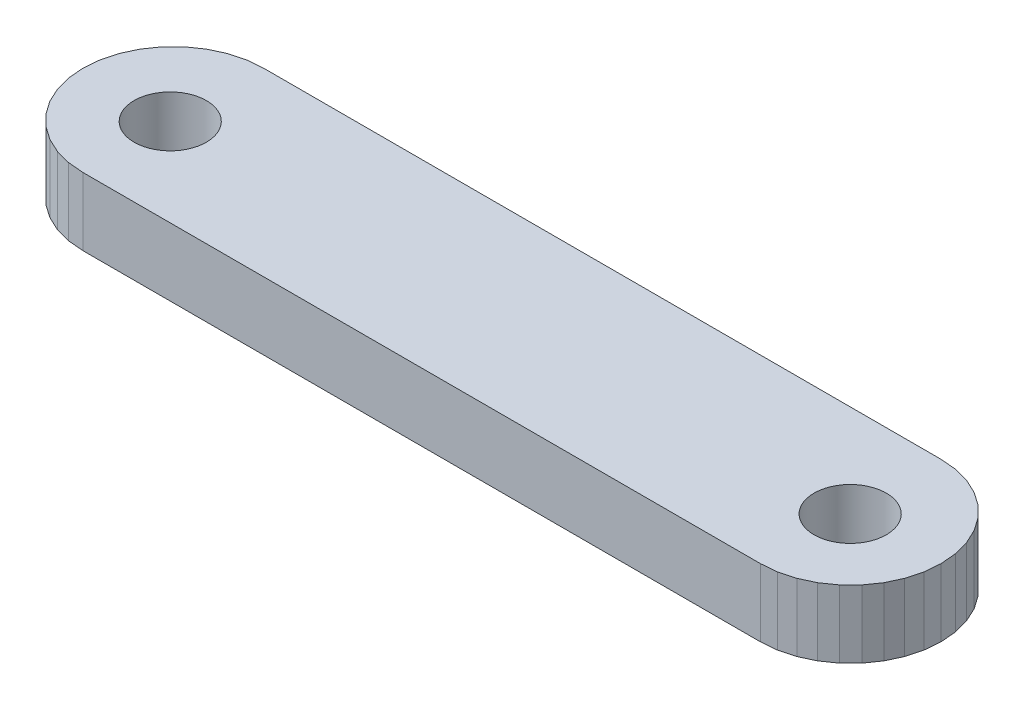
SolidWorks part; units mm, degrees
ref_plane "Front Plane" through (0, 0, 0) normal (0, 0, 1) x (1, 0, 0)
ref_plane "Top Plane" through (0, 0, 0) normal (0, 1, 0) x (1, 0, 0)
ref_plane "Right Plane" through (0, 0, 0) normal (1, 0, 0) x (0, 0, -1)
ref_plane "Plane1" through (0, 0, 0) normal (0, -1, 0) x (1, 0, 0)
sketch "Sketch1" plane through (0, 0, 0) normal (0, -1, 0) x (1, 0, 0)
  line L0 (3.3054, 0.0608) -> (4, 0)
  line L1 (4, 0) -> (34, 0)
  line L2 (34, 0) -> (34.6946, 0.0608)
  line L3 (34.6946, 0.0608) -> (35.3681, 0.2412)
  line L4 (35.3681, 0.2412) -> (36, 0.5359)
  line L5 (36, 0.5359) -> (36.5712, 0.9358)
  line L6 (36.5712, 0.9358) -> (37.0642, 1.4288)
  line L7 (37.0642, 1.4288) -> (37.4641, 2)
  line L8 (37.4641, 2) -> (37.7588, 2.6319)
  line L9 (37.7588, 2.6319) -> (37.9392, 3.3054)
  line L10 (37.9392, 3.3054) -> (38, 4)
  line L11 (38, 4) -> (37.9392, 4.6946)
  line L12 (37.9392, 4.6946) -> (37.7588, 5.3681)
  line L13 (37.7588, 5.3681) -> (37.4641, 6)
  line L14 (37.4641, 6) -> (37.0642, 6.5712)
  line L15 (37.0642, 6.5712) -> (36.5712, 7.0642)
  line L16 (36.5712, 7.0642) -> (36, 7.4641)
  line L17 (36, 7.4641) -> (35.3681, 7.7588)
  line L18 (35.3681, 7.7588) -> (34.6946, 7.9392)
  line L19 (34.6946, 7.9392) -> (34, 8)
  line L20 (34, 8) -> (4, 8)
  line L21 (4, 8) -> (3.3054, 7.9392)
  line L22 (3.3054, 7.9392) -> (2.6319, 7.7588)
  line L23 (2.6319, 7.7588) -> (2, 7.4641)
  line L24 (2, 7.4641) -> (1.4288, 7.0642)
  line L25 (1.4288, 7.0642) -> (0.9358, 6.5712)
  line L26 (0.9358, 6.5712) -> (0.5359, 6)
  line L27 (0.5359, 6) -> (0.2412, 5.3681)
  line L28 (0.2412, 5.3681) -> (0.0608, 4.6946)
  line L29 (0.0608, 4.6946) -> (0, 4)
  line L30 (0, 4) -> (0.0608, 3.3054)
  line L31 (0.0608, 3.3054) -> (0.2412, 2.6319)
  line L32 (0.2412, 2.6319) -> (0.5359, 2)
  line L33 (0.5359, 2) -> (0.9358, 1.4288)
  line L34 (0.9358, 1.4288) -> (1.4288, 0.9358)
  line L35 (1.4288, 0.9358) -> (2, 0.5359)
  line L36 (2, 0.5359) -> (2.6319, 0.2412)
  line L37 (2.6319, 0.2412) -> (3.3054, 0.0608)
  line L38 (32.3913, 2.6501) -> (32.1813, 2.95)
  line L39 (32.1813, 2.95) -> (32.0266, 3.2818)
  line L40 (32.0266, 3.2818) -> (31.9319, 3.6353)
  line L41 (31.9319, 3.6353) -> (31.9, 4)
  line L42 (31.9, 4) -> (31.9319, 4.3647)
  line L43 (31.9319, 4.3647) -> (32.0266, 4.7182)
  line L44 (32.0266, 4.7182) -> (32.1813, 5.05)
  line L45 (32.1813, 5.05) -> (32.3913, 5.3499)
  line L46 (32.3913, 5.3499) -> (32.6501, 5.6087)
  line L47 (32.6501, 5.6087) -> (32.95, 5.8187)
  line L48 (32.95, 5.8187) -> (33.2818, 5.9734)
  line L49 (33.2818, 5.9734) -> (33.6353, 6.0681)
  line L50 (33.6353, 6.0681) -> (34, 6.1)
  line L51 (34, 6.1) -> (34.3647, 6.0681)
  line L52 (34.3647, 6.0681) -> (34.7182, 5.9734)
  line L53 (34.7182, 5.9734) -> (35.05, 5.8187)
  line L54 (35.05, 5.8187) -> (35.3499, 5.6087)
  line L55 (35.3499, 5.6087) -> (35.6087, 5.3499)
  line L56 (35.6087, 5.3499) -> (35.8187, 5.05)
  line L57 (35.8187, 5.05) -> (35.9734, 4.7182)
  line L58 (35.9734, 4.7182) -> (36.0681, 4.3647)
  line L59 (36.0681, 4.3647) -> (36.1, 4)
  line L60 (36.1, 4) -> (36.0681, 3.6353)
  line L61 (36.0681, 3.6353) -> (35.9734, 3.2818)
  line L62 (35.9734, 3.2818) -> (35.8187, 2.95)
  line L63 (35.8187, 2.95) -> (35.6087, 2.6501)
  line L64 (35.6087, 2.6501) -> (35.3499, 2.3913)
  line L65 (35.3499, 2.3913) -> (35.05, 2.1813)
  line L66 (35.05, 2.1813) -> (34.7182, 2.0266)
  line L67 (34.7182, 2.0266) -> (34.3647, 1.9319)
  line L68 (34.3647, 1.9319) -> (34, 1.9)
  line L69 (34, 1.9) -> (33.6353, 1.9319)
  line L70 (33.6353, 1.9319) -> (33.2818, 2.0266)
  line L71 (33.2818, 2.0266) -> (32.95, 2.1813)
  line L72 (32.95, 2.1813) -> (32.6501, 2.3913)
  line L73 (32.6501, 2.3913) -> (32.3913, 2.6501)
  line L74 (5.6853, 2.5859) -> (5.4141, 2.3147)
  line L75 (5.4141, 2.3147) -> (5.1, 2.0947)
  line L76 (5.1, 2.0947) -> (4.7524, 1.9327)
  line L77 (4.7524, 1.9327) -> (4.382, 1.8334)
  line L78 (4.382, 1.8334) -> (4, 1.8)
  line L79 (4, 1.8) -> (3.618, 1.8334)
  line L80 (3.618, 1.8334) -> (3.2476, 1.9327)
  line L81 (3.2476, 1.9327) -> (2.9, 2.0947)
  line L82 (2.9, 2.0947) -> (2.5859, 2.3147)
  line L83 (2.5859, 2.3147) -> (2.3147, 2.5859)
  line L84 (2.3147, 2.5859) -> (2.0947, 2.9)
  line L85 (2.0947, 2.9) -> (1.9327, 3.2476)
  line L86 (1.9327, 3.2476) -> (1.8334, 3.618)
  line L87 (1.8334, 3.618) -> (1.8, 4)
  line L88 (1.8, 4) -> (1.8334, 4.382)
  line L89 (1.8334, 4.382) -> (1.9327, 4.7524)
  line L90 (1.9327, 4.7524) -> (2.0947, 5.1)
  line L91 (2.0947, 5.1) -> (2.3147, 5.4141)
  line L92 (2.3147, 5.4141) -> (2.5859, 5.6853)
  line L93 (2.5859, 5.6853) -> (2.9, 5.9053)
  line L94 (2.9, 5.9053) -> (3.2476, 6.0673)
  line L95 (3.2476, 6.0673) -> (3.618, 6.1666)
  line L96 (3.618, 6.1666) -> (4, 6.2)
  line L97 (4, 6.2) -> (4.382, 6.1666)
  line L98 (4.382, 6.1666) -> (4.7524, 6.0673)
  line L99 (4.7524, 6.0673) -> (5.1, 5.9053)
  line L100 (5.1, 5.9053) -> (5.4141, 5.6853)
  line L101 (5.4141, 5.6853) -> (5.6853, 5.4141)
  line L102 (5.6853, 5.4141) -> (5.9053, 5.1)
  line L103 (5.9053, 5.1) -> (6.0673, 4.7524)
  line L104 (6.0673, 4.7524) -> (6.1666, 4.382)
  line L105 (6.1666, 4.382) -> (6.2, 4)
  line L106 (6.2, 4) -> (6.1666, 3.618)
  line L107 (6.1666, 3.618) -> (6.0673, 3.2476)
  line L108 (6.0673, 3.2476) -> (5.9053, 2.9)
  line L109 (5.9053, 2.9) -> (5.6853, 2.5859)
extrude "Boss-Extrude1" add sketch "Sketch1" against normal blind 3
sketch "Sketch2" plane through (0, 3, 0) normal (0, 1, 0) x (1, 0, 0)
  circle A0 centre (3.9304, -4.1967) radius 2.7671
  circle A1 centre (34.1483, -4.1967) radius 3.0068
extrude "Boss-Extrude2" add sketch "Sketch2" against normal blind 3
hole_wizard "M3 Clearance Hole1" positions "Sketch3" profile "Sketch4" hole size "M3" standard "ANSI Metric" end condition through all
sketch "Sketch3" plane through (0, 3, 0) normal (0, 1, 0) x (1, 0, 0)
  point P0 (3.9744, -4.1083)
  point P2 (34.0836, -4.1083)
sketch "Sketch4" plane through (3.9744, 3, 4.1083) normal (1, 0, 0) x (0, 0, 1)
  line L0 (0, 0) -> (0, 3)
  line L1 (0, 3) -> (1.6, 3)
  line L2 (1.6, 3) -> (1.6, 0)
  line L5 (1.6, 0) -> (0, 0)
  line L11 (0, -6.35) -> (0, 107.95) construction
  dimension "Thru Hole Dia." = 3.2
  dimension "Thru Hole Depth" = 3
